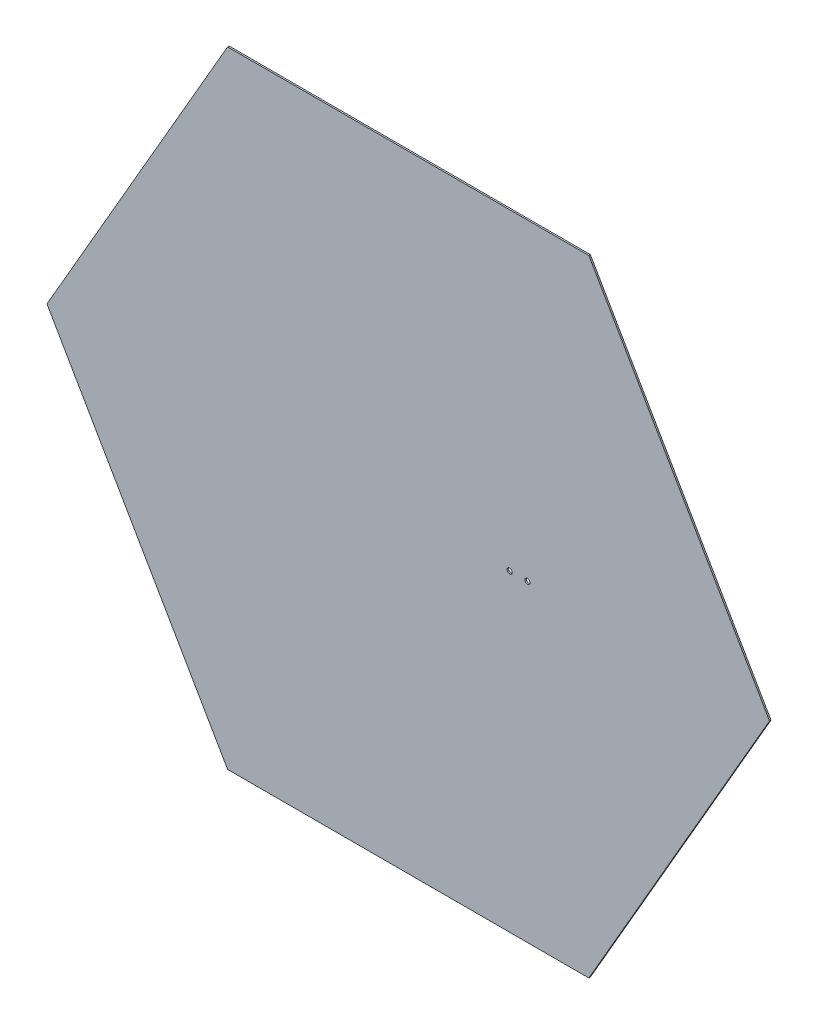
SolidWorks part; units mm, degrees
material "6063-T5"
ref_plane "Alzado" through (0, 0, 0) normal (0, 0, 1) x (1, 0, 0)
ref_plane "Planta" through (0, 0, 0) normal (0, 1, 0) x (1, 0, 0)
ref_plane "Vista lateral" through (0, 0, 0) normal (1, 0, 0) x (0, 0, -1)
sketch "Croquis1" plane through (0, 0, 0) normal (0, 0, 1) x (1, 0, 0)
  line L1 (-266, 191) -> (266, 191) construction
  line L2 (-266, 191) -> (-266, -191) construction
  line L3 (-266, -191) -> (266, -191) construction
  line L4 (266, 191) -> (266, -191) construction
  line L5 (-266, 191) -> (266, -191) construction
  line L6 (-266, -191) -> (266, 191) construction
  line L7 (194.3938, 336.7) -> (-194.3938, 336.7)
  line L8 (-194.3938, 336.7) -> (-388.7877, 0)
  line L9 (-388.7877, 0) -> (-194.3938, -336.7)
  line L10 (-194.3938, -336.7) -> (194.3938, -336.7)
  line L11 (194.3938, -336.7) -> (388.7877, 0)
  line L12 (388.7877, 0) -> (194.3938, 336.7)
  line L13 (-388.7877, 336.7) -> (388.7877, 336.7) construction
  line L14 (-388.7877, 336.7) -> (-388.7877, -336.7) construction
  line L15 (-388.7877, -336.7) -> (388.7877, -336.7) construction
  line L16 (388.7877, 336.7) -> (388.7877, -336.7) construction
  line L17 (-388.7877, 336.7) -> (388.7877, -336.7) construction
  line L18 (-388.7877, -336.7) -> (388.7877, 336.7) construction
  circle A0 centre (0, 0) radius 336.7 construction
  point P0 (0, 0)
  dimension "D3" = 673.4
  dimension "D1" = 382
  dimension "D2" = 532
extrude "Saliente-Extruir1" add sketch "Croquis1" along normal blind 1.65
sketch "Croquis2" plane through (0, 0, 0) normal (0, 0, -1) x (-1, 0, 0)
  line L4 (-141.7986, 336.7) -> (-141.7986, -336.7) construction
  line L7 (388.7877, 0) -> (-388.7877, 0) construction
  line L8 (-194.3938, 336.7) -> (194.3938, 336.7) construction
  line L9 (194.3938, -336.7) -> (-194.3938, -336.7) construction
  circle A0 centre (-128.25, 0) radius 2.75
  circle A1 centre (-109.15, 0) radius 2.75
  dimension "D2" = 5.5
  dimension "D1" = 246.9891
  dimension "D3" = 19.1
extrude "Cortar-Extruir1" cut sketch "Croquis2" against normal through all
